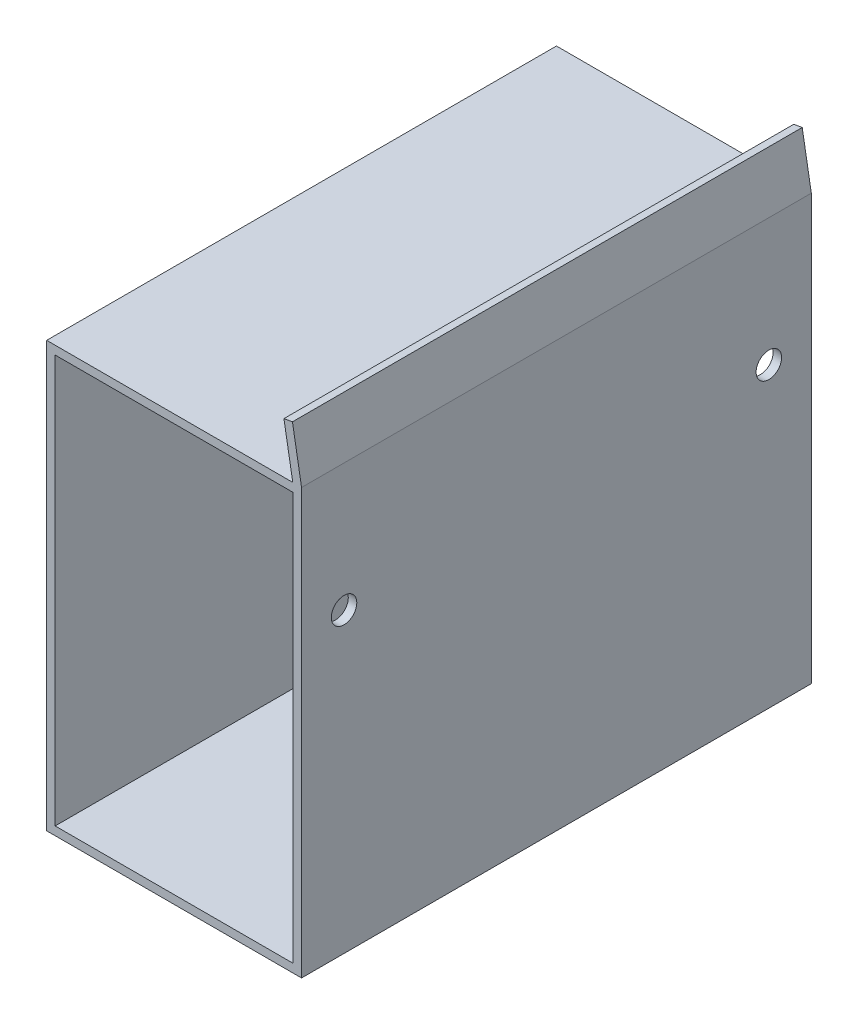
SolidWorks part; units mm, degrees
ref_plane "Plano frontal" through (0, 0, 0) normal (0, 0, 1) x (1, 0, 0)
ref_plane "Plano superior" through (0, 0, 0) normal (0, 1, 0) x (1, 0, 0)
ref_plane "Plano direito" through (0, 0, 0) normal (1, 0, 0) x (0, 0, -1)
sketch "Esboço1" plane through (0, 0, 0) normal (0, 0, 1) x (1, 0, 0)
  line L1 (0, 0) -> (-30, 0)
  line L2 (0, 0) -> (0, 50)
  line L3 (0, 50) -> (-30, 50)
  line L4 (-30, 0) -> (-30, 50)
extrude "Extrusão-Fina1" add sketch "Esboço1" along normal blind 60 thin
sketch "Esboço2" plane through (0, 0, 0) normal (0, 0, -1) x (-1, 0, 0)
  line L0 (0, 50) -> (1.0713, 56.158)
  line L1 (1.0713, 56.158) -> (2.0753, 55.9833)
  line L2 (2.0753, 55.9833) -> (1.0344, 50)
  line L3 (0, 50) -> (30, 50) construction
  line L4 (1.0344, 50) -> (0, 50)
extrude "Ressalto-extrusão1" add sketch "Esboço2" against normal through all
sketch "Esboço3" plane through (0, 0, 0) normal (1, 0, 0) x (0, 0, -1)
  circle A0 centre (-55, 35) radius 1.5
  circle A1 centre (-5, 35) radius 1.5
extrude "Corte-extrusão1" cut sketch "Esboço3" against normal blind 10
